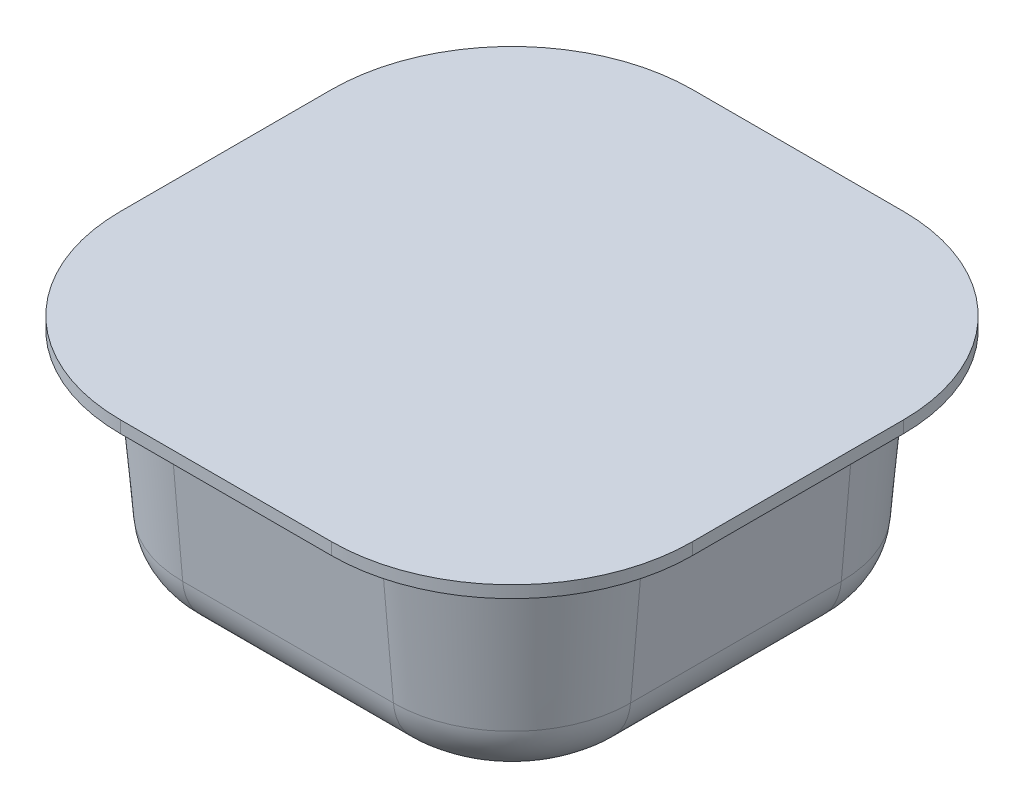
SolidWorks part; units mm, degrees
ref_plane "Front Plane" through (0, 0, 0) normal (0, 0, 1) x (1, 0, 0)
ref_plane "Top Plane" through (0, 0, 0) normal (0, 1, 0) x (1, 0, 0)
ref_plane "Right Plane" through (0, 0, 0) normal (1, 0, 0) x (0, 0, -1)
ref_plane "Plane1" through (0, 19.05, 0) normal (0, 1, 0) x (1, 0, 0)
sketch "Sketch1" plane through (0, 19.05, 0) normal (0, 1, 0) x (1, 0, 0)
  line L1 (24.13, 24.13) -> (-24.13, 24.13)
  line L2 (24.13, 24.13) -> (24.13, -24.13)
  line L3 (24.13, -24.13) -> (-24.13, -24.13)
  line L4 (-24.13, 24.13) -> (-24.13, -24.13)
  line L5 (24.13, 24.13) -> (-24.13, -24.13) construction
  line L6 (24.13, -24.13) -> (-24.13, 24.13) construction
  point P0 (0, 0)
  dimension "D1" = 48.26
extrude "Boss-Extrude1" add sketch "Sketch1" against normal blind 1.016
fillet "Fillet1" radius 15.24 4 edges at (-24.13, 18.542, 24.13) (24.13, 18.542, -24.13) (-24.13, 18.542, -24.13) (24.13, 18.542, 24.13)
sketch "Sketch2" plane through (0, 18.034, 0) normal (0, -1, 0) x (1, 0, 0)
  line L8 (8.89, 20.066) -> (-8.89, 20.066)
  line L9 (-20.066, 8.89) -> (-20.066, -8.89)
  line L10 (-8.89, -20.066) -> (8.89, -20.066)
  line L11 (20.066, -8.89) -> (20.066, 8.89)
  line L12 (8.89, 20.066) -> (-8.89, 20.066)
  line L13 (-20.066, 8.89) -> (-20.066, -8.89)
  line L14 (-8.89, -20.066) -> (8.89, -20.066)
  line L15 (20.066, -8.89) -> (20.066, 8.89)
  arc A8 (-8.89, 20.066) -> (-20.066, 8.89) centre (-8.89, 8.89) ccw
  arc A9 (-20.066, -8.89) -> (-8.89, -20.066) centre (-8.89, -8.89) ccw
  arc A10 (8.89, -20.066) -> (20.066, -8.89) centre (8.89, -8.89) ccw
  arc A11 (20.066, 8.89) -> (8.89, 20.066) centre (8.89, 8.89) ccw
  arc A12 (-8.89, 20.066) -> (-20.066, 8.89) centre (-8.89, 8.89) ccw
  arc A13 (-20.066, -8.89) -> (-8.89, -20.066) centre (-8.89, -8.89) ccw
  arc A14 (8.89, -20.066) -> (20.066, -8.89) centre (8.89, -8.89) ccw
  arc A15 (20.066, 8.89) -> (8.89, 20.066) centre (8.89, 8.89) ccw
  dimension "D1" = 4.064
extrude "Boss-Extrude2" add sketch "Sketch2" along normal up to surface (18.034 mm away) draft 5
fillet "Fillet2" radius 5.08 8 edges at (15.677, 0, 15.677) (0, 0, 18.4882) (-15.677, 0, 15.677) (-18.4882, 0, 0) (-15.677, 0, -15.677) (0, 0, -18.4882) (15.677, 0, -15.677) (18.4882, 0, 0)
sketch "Sketch3" plane through (0, 19.05, 0) normal (0, 1, 0) x (1, 0, 0)
  line L4 (-24.13, 8.89) -> (-24.13, -8.89)
  line L5 (-8.89, -24.13) -> (8.89, -24.13)
  line L6 (24.13, -8.89) -> (24.13, 8.89)
  line L7 (8.89, 24.13) -> (-8.89, 24.13)
  line L8 (-24.13, 8.89) -> (-24.13, -8.89)
  line L9 (-8.89, -24.13) -> (8.89, -24.13)
  line L10 (24.13, -8.89) -> (24.13, 8.89)
  line L11 (8.89, 24.13) -> (-8.89, 24.13)
  arc A4 (-24.13, -8.89) -> (-8.89, -24.13) centre (-8.89, -8.89) ccw
  arc A5 (8.89, -24.13) -> (24.13, -8.89) centre (8.89, -8.89) ccw
  arc A6 (24.13, 8.89) -> (8.89, 24.13) centre (8.89, 8.89) ccw
  arc A7 (-8.89, 24.13) -> (-24.13, 8.89) centre (-8.89, 8.89) ccw
  arc A8 (-24.13, -8.89) -> (-8.89, -24.13) centre (-8.89, -8.89) ccw
  arc A9 (8.89, -24.13) -> (24.13, -8.89) centre (8.89, -8.89) ccw
  arc A10 (24.13, 8.89) -> (8.89, 24.13) centre (8.89, 8.89) ccw
  arc A11 (-8.89, 24.13) -> (-24.13, 8.89) centre (-8.89, 8.89) ccw
  dimension "D1" = 0
